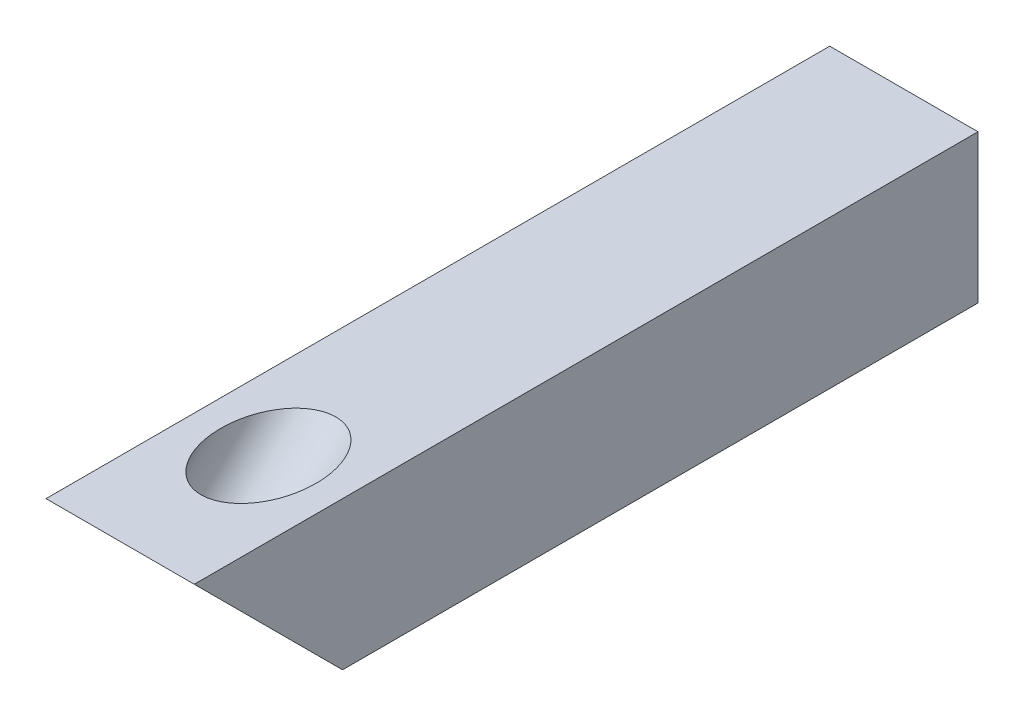
SolidWorks part; units mm, degrees
ref_plane "Front Plane" through (0, 0, 0) normal (0, 0, 1) x (1, 0, 0)
ref_plane "Top Plane" through (0, 0, 0) normal (0, 1, 0) x (1, 0, 0)
ref_plane "Right Plane" through (0, 0, 0) normal (1, 0, 0) x (0, 0, -1)
sketch "Sketch1" plane through (0, 0, 0) normal (0, 0, 1) x (1, 0, 0)
  line L1 (0, 0) -> (7, 0)
  line L2 (0, 0) -> (0, 7)
  line L3 (0, 7) -> (7, 7)
  line L4 (7, 0) -> (7, 7)
  dimension "D1" = 7
  dimension "D2" = 7
extrude "Boss-Extrude1" add sketch "Sketch1" along normal blind 20
sketch "Sketch3" plane through (7, 0, 0) normal (1, 0, 0) x (0, 0, -1)
  line L0 (-20, 7) -> (-27, 7)
  line L1 (-27, 7) -> (-20, 0)
  line L2 (-20, 0) -> (-20, 7)
extrude "Boss-Extrude2" add sketch "Sketch3" against normal blind 7
sketch "Sketch4" plane through (0, -10, 10) normal (0, -0.7071, 0.7071) x (1, 0, 0)
  circle A0 centre (3.5, 19.0919) radius 2.25
  dimension "D1" = 4.5
sketch "Sketch5" plane through (0, 0, 0) normal (0, 0, -1) x (-1, 0, 0)
  line L1 (-7, 0) -> (0, 0)
  line L2 (-7, 0) -> (-7, 7)
  line L3 (-7, 7) -> (0, 7)
  line L4 (0, 0) -> (0, 7)
extrude "Boss-Extrude4" add sketch "Sketch5" along normal blind 10
extrude "Cut-Extrude1" cut sketch "Sketch4" against normal through all
